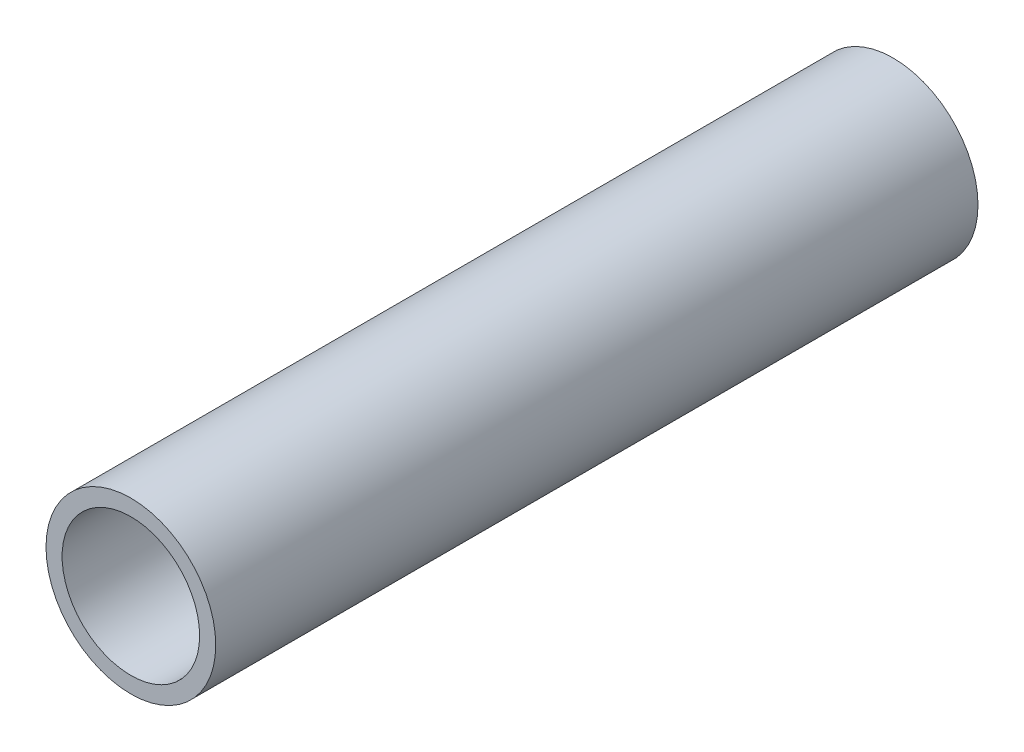
SolidWorks part; units mm, degrees
material "PVC Rigid"
ref_plane "Front Plane" through (0, 0, 0) normal (0, 0, 1) x (1, 0, 0)
ref_plane "Top Plane" through (0, 0, 0) normal (0, 1, 0) x (1, 0, 0)
ref_plane "Right Plane" through (0, 0, 0) normal (1, 0, 0) x (0, 0, -1)
sketch "Sketch1" plane through (0, 0, 0) normal (0, 0, 1) x (1, 0, 0)
  circle A0 centre (0, 0) radius 16.7
  circle A1 centre (0, 0) radius 13.53
  dimension "D1" = 33.4
  dimension "D2" = 3.17
extrude "Boss-Extrude1" add sketch "Sketch1" along normal blind 150
